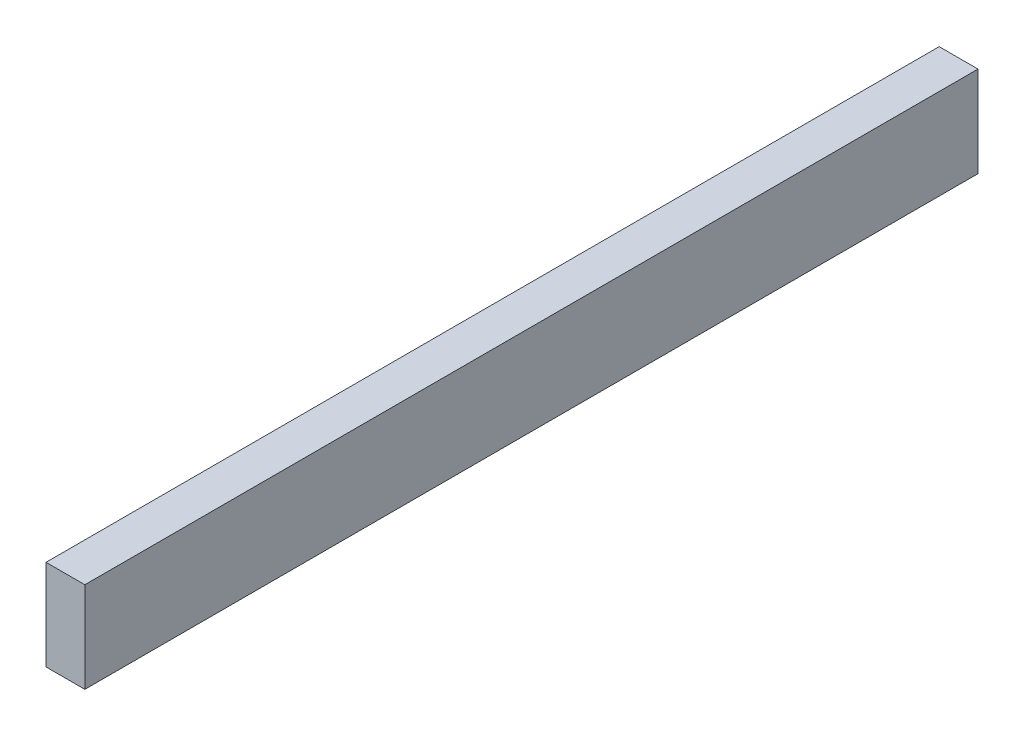
SolidWorks part; units mm, degrees
material "Pine"
ref_plane "Front Plane" through (0, 0, 0) normal (0, 0, 1) x (1, 0, 0)
ref_plane "Top Plane" through (0, 0, 0) normal (0, 1, 0) x (1, 0, 0)
ref_plane "Right Plane" through (0, 0, 0) normal (1, 0, 0) x (0, 0, -1)
sketch "Sketch1" plane through (0, 0, 0) normal (0, 0, 1) x (1, 0, 0)
  line L1 (-19.05, -44.45) -> (19.05, -44.45)
  line L2 (-19.05, -44.45) -> (-19.05, 44.45)
  line L3 (-19.05, 44.45) -> (19.05, 44.45)
  line L4 (19.05, -44.45) -> (19.05, 44.45)
  line L5 (-19.05, -44.45) -> (19.05, 44.45) construction
  line L6 (-19.05, 44.45) -> (19.05, -44.45) construction
  point P0 (0, 0)
  dimension "D1" = 88.9
  dimension "D2" = 38.1
extrude "Boss-Extrude1" add sketch "Sketch1" along normal blind 876.3
